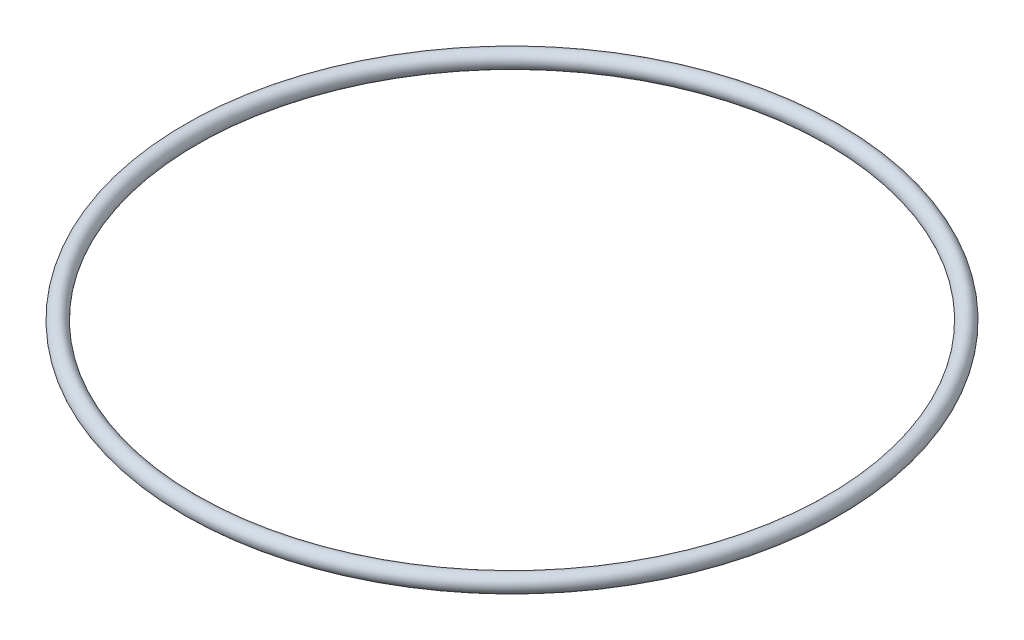
SolidWorks part; units mm, degrees
ref_plane "Front Plane" through (0, 0, 0) normal (0, 0, 1) x (1, 0, 0)
ref_plane "Top Plane" through (0, 0, 0) normal (0, 1, 0) x (1, 0, 0)
ref_plane "Right Plane" through (0, 0, 0) normal (1, 0, 0) x (0, 0, -1)
sketch "Sketch1" plane through (0, 0, 0) normal (0, 0, 1) x (1, 0, 0)
  line L0 (-8.4478, 0) -> (46.101, 0) construction
  line L1 (0, 0) -> (0, 22.0795) construction
  circle A0 centre (46.101, 0) radius 1.1906
  dimension "D1" = 2.3813
  dimension "D2" = 46.101
revolve "Revolve1" add sketch "Sketch1" angle 360 about L1
